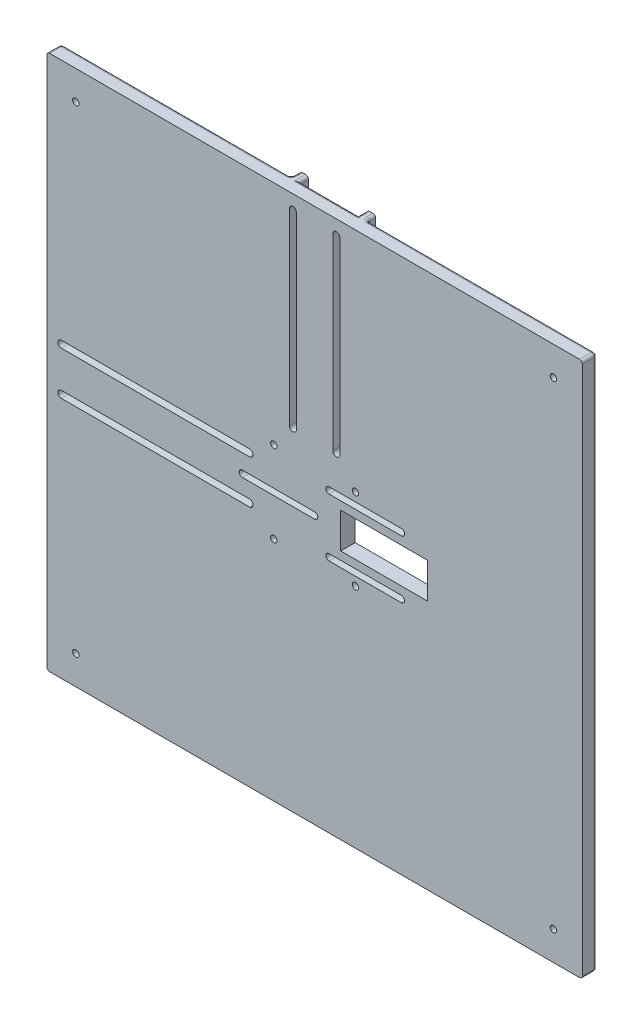
SolidWorks part; units mm, degrees
ref_plane "Plan de face" through (0, 0, 0) normal (0, 0, 1) x (1, 0, 0)
ref_plane "Plan de dessus" through (0, 0, 0) normal (0, 1, 0) x (1, 0, 0)
ref_plane "Plan de droite" through (0, 0, 0) normal (1, 0, 0) x (0, 0, -1)
sketch "Esquisse1" plane through (0, 0, 0) normal (0, 0, 1) x (1, 0, 0)
  line L1 (-92.5, 92.5) -> (92.5, 92.5)
  line L2 (-92.5, 92.5) -> (-92.5, -92.5)
  line L3 (-92.5, -92.5) -> (92.5, -92.5)
  line L4 (92.5, 92.5) -> (92.5, -92.5)
  dimension "D1" = 185
  dimension "D2" = 185
  dimension "D3" = 92.5
  dimension "D4" = 92.5
extrude "Boss.-Extru.1" add sketch "Esquisse1" along normal blind 5
sketch "Esquisse2" plane through (0, 0, 0) normal (0, 0, -1) x (-1, 0, 0)
  line L1 (22.5, 10.1) -> (92.5, 10.1)
  line L4 (92.5, 10.1) -> (92.5, 13.1)
  line L5 (92.5, -13.1) -> (22.5, -13.1)
  line L6 (92.5, -13.1) -> (92.5, -10.1)
  line L7 (92.5, -10.1) -> (22.5, -10.1)
  line L19 (92.5, 92.5) -> (92.5, -92.5) construction
  line L24 (13.1, 22.5) -> (13.1, 92.5)
  line L25 (-92.5, 92.5) -> (92.5, 92.5) construction
  line L26 (10.1, 22.5) -> (10.1, 92.5)
  line L28 (-13.1, 92.5) -> (-10.1, 92.5)
  line L29 (10.1, 92.5) -> (13.1, 92.5)
  line L31 (-10.1, 92.5) -> (-10.1, 22.5)
  line L32 (-13.1, 92.5) -> (-13.1, 22.5)
  line L33 (-10.1, 22.5) -> (-13.1, 22.5)
  line L35 (22.5, -10.1) -> (22.5, -13.1)
  line L36 (92.5, 13.1) -> (22.5, 13.1)
  line L37 (22.5, 13.1) -> (22.5, 10.1)
  line L38 (13.1, 22.5) -> (10.1, 22.5)
  dimension "D1" = 20.2
  dimension "D2" = 3
  dimension "D3" = 3
  dimension "D4" = 10.1
  dimension "D5" = 3
  dimension "D6" = 3
  dimension "D7" = 20.2
  dimension "D8" = 10.1
  dimension "D9" = 70
  dimension "D10" = 70
extrude "Boss.-Extru.2" add sketch "Esquisse2" along normal blind 3
fillet "Congé1" radius 1 32 edges at (-13.1, 57.5, 0) (-57.5, -13.1, 0) (-13.1, 92.5, -1.5) (-92.5, -13.1, -1.5) (92.5, -92.5, 2.5) (92.5, 92.5, 2.5) (92.5, 0, 0) (0, 92.5, 0) (-92.5, 0, 0) (-52.8, 92.5, 0) (-92.5, 52.8, 0) (-92.5, 92.5, 2.5) (52.8, 92.5, 0) (0, -92.5, 0) (-92.5, -52.8, 0) (-92.5, -92.5, 2.5) (-10.1, 92.5, -1.5) (-92.5, 10.1, -1.5) (-92.5, -10.1, -1.5) (13.1, 92.5, -1.5) (10.1, 92.5, -1.5) (13.1, 57.5, 0) (-92.5, 13.1, -1.5) (-57.5, 13.1, 0) (-22.5, -11.6, 0) (11.6, 22.5, 0) (-11.6, 22.5, 0) (-22.5, 11.6, 0) (-22.5, -13.1, -1.5) (13.1, 22.5, -1.5) (-13.1, 22.5, -1.5) (-22.5, 13.1, -1.5)
sketch "Esquisse4" plane through (0, 0, 0) normal (0, 0, -1) x (-1, 0, 0)
  line L4 (-92.5, -91.5) -> (-92.5, 91.5) construction
  line L5 (91.5, -92.5) -> (-91.5, -92.5) construction
  line L6 (-91.5, 92.5) -> (-14.1, 92.5) construction
  line L7 (92.5, -14.1) -> (92.5, -91.5) construction
  circle A0 centre (-14.1, 14.1) radius 1.1
  circle A1 centre (14.1, 14.1) radius 1.1
  circle A2 centre (14.1, -14.1) radius 1.1
  circle A3 centre (-14.1, -14.1) radius 1.1
  circle A4 centre (-82.5, -82.5) radius 1.1
  circle A5 centre (-82.5, 82.5) radius 1.1
  circle A6 centre (82.5, -82.5) radius 1.1
  circle A7 centre (82.5, 82.5) radius 1.1
  dimension "D1" = 2.2
  dimension "D4" = 4
  dimension "D5" = 4
  dimension "D6" = 10
  dimension "D7" = 10
  dimension "D8" = 10
  dimension "D9" = 10
  dimension "D10" = 4
  dimension "D11" = 4
extrude "Enlèv. mat.-Extru.1" cut sketch "Esquisse4" against normal up to next
sketch "Esquisse5" plane through (0, 0, 0) normal (0, 0, -1) x (-1, 0, 0)
  line L0 (-7.5, 87.5) -> (-7.5, 22.5) construction
  line L1 (-6.3, 87.5) -> (-6.3, 22.5)
  line L2 (-8.7, 87.5) -> (-8.7, 22.5)
  line L3 (7.5, 87.5) -> (7.5, 22.5) construction
  line L4 (8.7, 87.5) -> (8.7, 22.5)
  line L5 (6.3, 87.5) -> (6.3, 22.5)
  line L9 (10.1, 91.5) -> (10.1, 21.5) construction
  line L10 (-10.1, 92.5) -> (10.1, 92.5) construction
  line L11 (-10.1, 21.5) -> (-10.1, 91.5) construction
  line L12 (-91.5, 92.5) -> (-14.1, 92.5) construction
  arc A0 (-6.3, 87.5) -> (-8.7, 87.5) centre (-7.5, 87.5) ccw
  arc A1 (-8.7, 22.5) -> (-6.3, 22.5) centre (-7.5, 22.5) ccw
  arc A2 (8.7, 87.5) -> (6.3, 87.5) centre (7.5, 87.5) ccw
  arc A3 (6.3, 22.5) -> (8.7, 22.5) centre (7.5, 22.5) ccw
  point P2 (-7.5, 55)
  point P7 (7.5, 55)
  dimension "D1" = 1.2
  dimension "D2" = 1.2
  dimension "D3" = 2.6
  dimension "D4" = 5
  dimension "D6" = 2.6
  dimension "D7" = 70
extrude "Enlèv. mat.-Extru.2" cut sketch "Esquisse5" against normal through all
sketch "Esquisse6" plane through (0, 0, 0) normal (0, 0, -1) x (-1, 0, 0)
  line L0 (87.5, -7.5) -> (22.5, -7.5) construction
  line L1 (87.5, -8.7) -> (22.5, -8.7)
  line L2 (87.5, -6.3) -> (22.5, -6.3)
  line L3 (22.5, 7.5) -> (87.5, 7.5) construction
  line L4 (22.5, 8.7) -> (87.5, 8.7)
  line L5 (22.5, 6.3) -> (87.5, 6.3)
  line L6 (91.5, -10.1) -> (21.5, -10.1) construction
  line L7 (21.5, 10.1) -> (91.5, 10.1) construction
  line L8 (92.5, 10.1) -> (92.5, -10.1) construction
  arc A0 (87.5, -8.7) -> (87.5, -6.3) centre (87.5, -7.5) ccw
  arc A1 (22.5, -6.3) -> (22.5, -8.7) centre (22.5, -7.5) ccw
  arc A2 (22.5, 8.7) -> (22.5, 6.3) centre (22.5, 7.5) ccw
  arc A3 (87.5, 6.3) -> (87.5, 8.7) centre (87.5, 7.5) ccw
  point P2 (55, -7.5)
  point P7 (55, 7.5)
  dimension "D1" = 1.2
  dimension "D2" = 1.2
  dimension "D3" = 2.6
  dimension "D4" = 2.6
  dimension "D5" = 5
  dimension "D7" = 70
extrude "Enlèv. mat.-Extru.3" cut sketch "Esquisse6" against normal up to next
sketch "Esquisse9" plane through (0, 0, 5) normal (0, 0, 1) x (1, 0, 0)
  line L0 (-25, 0) -> (0, 0) construction
  line L1 (-25, 1.1) -> (0, 1.1)
  line L2 (-25, -1.1) -> (0, -1.1)
  line L3 (5, 10) -> (30, 10) construction
  line L4 (5, 11.1) -> (30, 11.1)
  line L5 (5, 8.9) -> (30, 8.9)
  line L6 (5, -10) -> (30, -10) construction
  line L7 (5, -8.9) -> (30, -8.9)
  line L8 (5, -11.1) -> (30, -11.1)
  arc A0 (-25, 1.1) -> (-25, -1.1) centre (-25, 0) ccw
  arc A1 (0, -1.1) -> (0, 1.1) centre (0, 0) ccw
  arc A2 (5, 11.1) -> (5, 8.9) centre (5, 10) ccw
  arc A3 (30, 8.9) -> (30, 11.1) centre (30, 10) ccw
  arc A4 (5, -8.9) -> (5, -11.1) centre (5, -10) ccw
  arc A5 (30, -11.1) -> (30, -8.9) centre (30, -10) ccw
  point P3 (-12.5, 0)
  point P8 (17.5, 10)
  point P15 (17.5, -10)
  point P22 (0, 0)
  dimension "D4" = 25
  dimension "D5" = 30
  dimension "D1" = 2.2
  dimension "D2" = 2.2
  dimension "D3" = 2.2
  dimension "D6" = 25
  dimension "D7" = 10
  dimension "D8" = 10
  dimension "D9" = 25
extrude "Enlèv. mat.-Extru.5" cut sketch "Esquisse9" against normal up to next
sketch "Esquisse11" plane through (0, 0, 0) normal (0, 0, -1) x (-1, 0, 0)
  line L1 (-9, 6.1) -> (-39, 6.1)
  line L2 (-9, 6.1) -> (-9, -6.1)
  line L3 (-9, -6.1) -> (-39, -6.1)
  line L4 (-39, 6.1) -> (-39, -6.1)
  dimension "D1" = 9
  dimension "D2" = 12.2
  dimension "D3" = 6.1
  dimension "D4" = 30
extrude "Enlèv. mat.-Extru.7" cut sketch "Esquisse11" against normal up to next
sketch "Esquisse12" plane through (0, 0, 0) normal (0, 0, -1) x (-1, 0, 0)
  line L1 (-33, 12.1) -> (-2, 12.1)
  line L2 (-33, 12.1) -> (-33, 7.8)
  line L3 (-33, 7.8) -> (-2, 7.8)
  line L4 (-2, 12.1) -> (-2, 7.8)
  line L5 (-33, -7.9) -> (-2, -7.9)
  line L6 (-33, -7.9) -> (-33, -12.2)
  line L7 (-33, -12.2) -> (-2, -12.2)
  line L8 (-2, -7.9) -> (-2, -12.2)
  line L9 (-3, 2.1) -> (28, 2.1)
  line L10 (-3, 2.1) -> (-3, -2.2)
  line L11 (-3, -2.2) -> (28, -2.2)
  line L12 (28, 2.1) -> (28, -2.2)
  arc A0 (-30, 11.1) -> (-30, 8.9) centre (-30, 10) ccw construction
  arc A1 (-30, -8.9) -> (-30, -11.1) centre (-30, -10) ccw construction
  arc A2 (-5, -11.1) -> (-5, -8.9) centre (-5, -10) ccw construction
  arc A3 (0, 1.1) -> (0, -1.1) centre (0, 0) ccw construction
  arc A4 (25, -1.1) -> (25, 1.1) centre (25, 0) ccw construction
  arc A5 (-5, 8.9) -> (-5, 11.1) centre (-5, 10) ccw construction
  point P15 (-31.1, 10)
  point P20 (-31.1, -10)
  dimension "D7" = 3
  dimension "D8" = 3
  dimension "D9" = 3
  dimension "D10" = 3
  dimension "D11" = 3
  dimension "D12" = 3
  dimension "D1" = 2.1
  dimension "D2" = 4.3
  dimension "D3" = 2.1
  dimension "D4" = 4.3
  dimension "D5" = 2.1
  dimension "D6" = 4.3
extrude "Enlèv. mat.-Extru.9" cut sketch "Esquisse12" against normal blind 2
fillet "Congé2" radius 0.5 11 edges at (33, -12.2, 1) (33, -7.9, 1) (2, -7.9, 1) (2, -12.2, 1) (-28, -2.2, 1) (-28, 2.1, 1) (3, -2.2, 1) (3, 2.1, 1) (2, 12.1, 1) (33, 7.8, 1) (33, 12.1, 1)
sketch "Esquisse13" plane through (0, 0, 0) normal (0, 0, -1) x (-1, 0, 0)
  line L0 (-14.1, 91.5) -> (-91.5, 91.5) construction
  line L1 (-80, -82.5) -> (-81.25, -80.3349)
  line L2 (-81.25, -80.3349) -> (-83.75, -80.3349)
  line L3 (-83.75, -80.3349) -> (-85, -82.5)
  line L4 (-85, -82.5) -> (-83.75, -84.6651)
  line L5 (-83.75, -84.6651) -> (-81.25, -84.6651)
  line L6 (-81.25, -84.6651) -> (-80, -82.5)
  line L7 (83.75, -84.6651) -> (85, -82.5)
  line L8 (85, -82.5) -> (83.75, -80.3349)
  line L9 (83.75, -80.3349) -> (81.25, -80.3349)
  line L10 (81.25, -80.3349) -> (80, -82.5)
  line L11 (80, -82.5) -> (81.25, -84.6651)
  line L12 (81.25, -84.6651) -> (83.75, -84.6651)
  line L13 (85, 82.5) -> (83.75, 84.6651)
  line L14 (83.75, 84.6651) -> (81.25, 84.6651)
  line L15 (81.25, 84.6651) -> (80, 82.5)
  line L16 (80, 82.5) -> (81.25, 80.3349)
  line L17 (81.25, 80.3349) -> (83.75, 80.3349)
  line L18 (83.75, 80.3349) -> (85, 82.5)
  line L19 (-80, 82.5) -> (-81.25, 84.6651)
  line L20 (-81.25, 84.6651) -> (-83.75, 84.6651)
  line L21 (-83.75, 84.6651) -> (-85, 82.5)
  line L22 (-85, 82.5) -> (-83.75, 80.3349)
  line L23 (-83.75, 80.3349) -> (-81.25, 80.3349)
  line L24 (-81.25, 80.3349) -> (-80, 82.5)
  line L25 (91.5, 91.5) -> (14.1, 91.5) construction
  line L26 (-91.5, -91.5) -> (91.5, -91.5) construction
  circle A0 centre (-82.5, -82.5) radius 2.1651 construction
  circle A1 centre (82.5, -82.5) radius 2.1651 construction
  circle A2 centre (82.5, 82.5) radius 2.1651 construction
  circle A3 centre (-82.5, 82.5) radius 2.1651 construction
  dimension "D1" = 2.5
  dimension "D2" = 2.5
  dimension "D3" = 2.5
  dimension "D4" = 2.5
extrude "Enlèv. mat.-Extru.10" cut sketch "Esquisse13" against normal blind 3
